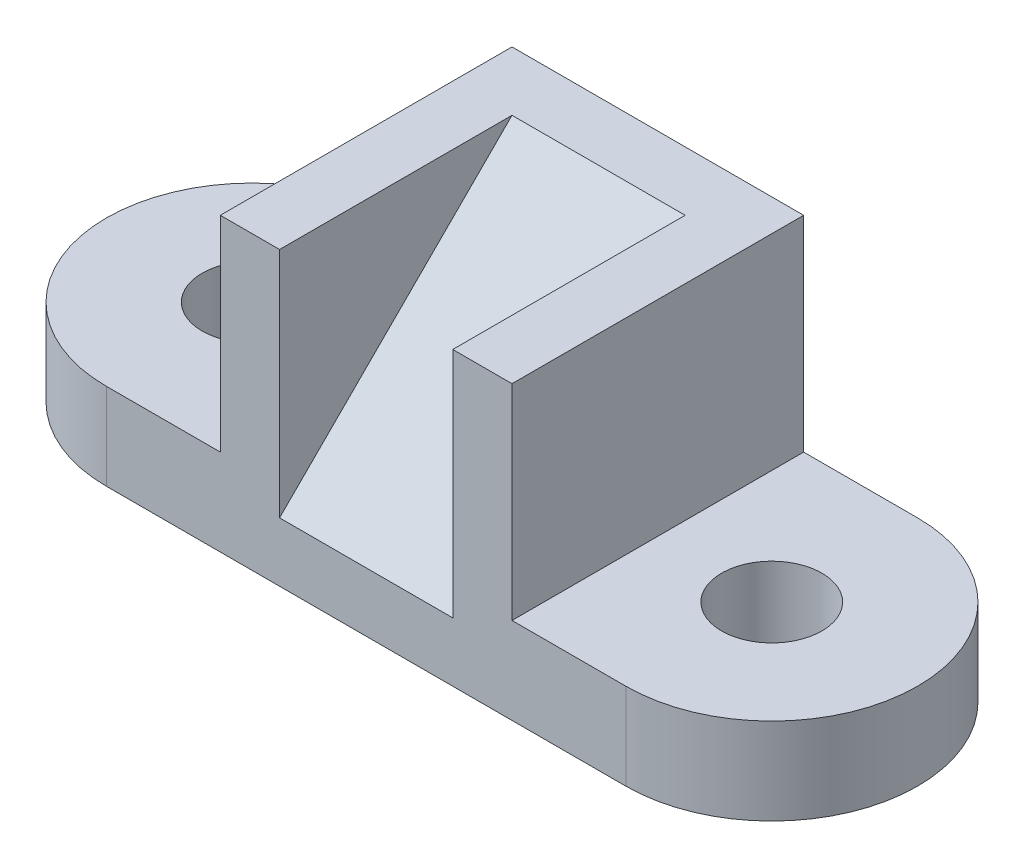
SolidWorks part; units mm, degrees
ref_plane "Front Plane" through (0, 0, 0) normal (0, 0, 1) x (1, 0, 0)
ref_plane "Top Plane" through (0, 0, 0) normal (0, 1, 0) x (1, 0, 0)
ref_plane "Right Plane" through (0, 0, 0) normal (1, 0, 0) x (0, 0, -1)
sketch "Sketch1" plane through (0, 0, 0) normal (0, 1, 0) x (1, 0, 0)
  line L0 (0, 0) -> (114, 0) construction
  line L1 (0, 32) -> (114, 32)
  line L2 (0, -32) -> (114, -32)
  arc A0 (0, 32) -> (0, -32) centre (0, 0) ccw
  arc A1 (114, -32) -> (114, 32) centre (114, 0) ccw
  dimension "D1" = 64
  dimension "D2" = 114
extrude "Boss-Extrude1" add sketch "Sketch1" along normal blind 19
sketch "Sketch2" plane through (0, 19, 0) normal (0, 1, 0) x (1, 0, 0)
  line L0 (0, 0) -> (114, 0) construction
  circle A0 centre (0, 0) radius 11
  circle A1 centre (114, 0) radius 11
  dimension "D1" = 22
  dimension "D2" = 114
extrude "Cut-Extrude1" cut sketch "Sketch2" against normal blind 19
sketch "Sketch3" plane through (0, 19, 0) normal (0, 1, 0) x (1, 0, 0)
  line L0 (-32, 0) -> (146, 0) construction
  line L1 (57, 32) -> (57, -32) construction
  line L2 (0, -32) -> (114, -32) construction
  line L3 (89, 32) -> (89, -32)
  line L4 (89, 32) -> (25, 32)
  line L6 (89, -32) -> (25, -32)
  line L7 (25, 32) -> (25, -32)
  arc A0 (0, 32) -> (0, -32) centre (0, 0) ccw construction
  arc A1 (114, -32) -> (114, 32) centre (114, 0) ccw construction
  point P13 (57, 0)
  dimension "D1" = 64
extrude "Boss-Extrude2" add sketch "Sketch3" along normal blind 45
sketch "Sketch4" plane through (0, 0, 32) normal (0, 0, 1) x (1, 0, 0)
  line L0 (25, 64) -> (38, 64) construction
  line L1 (25, 64) -> (89, 64) construction
  line L2 (25, 41.5) -> (89, 41.5) construction
  line L3 (25, 64) -> (25, 19) construction
  line L4 (89, 64) -> (89, 19) construction
  line L5 (57, 64) -> (57, 41.5) construction
  line L6 (57, 41.5) -> (57, 0) construction
  line L7 (0, 0) -> (114, 0) construction
  line L8 (89, 64) -> (76, 64) construction
  line L9 (89, 0) -> (89, 13) construction
  line L11 (38, 64) -> (76, 64)
  line L12 (38, 64) -> (38, 13)
  line L13 (38, 13) -> (76, 13)
  line L14 (76, 64) -> (76, 13)
  dimension "D1" = 38
  dimension "D2" = 51
sketch "Sketch5" plane through (0, 64, 0) normal (0, 1, 0) x (1, 0, 0)
  line L0 (57, 32) -> (57, 19) construction
  line L1 (89, 32) -> (25, 32) construction
  line L2 (25, 0) -> (38, 0) construction
  line L3 (25, 32) -> (25, -32) construction
  line L4 (89, 0) -> (76, 0) construction
  line L5 (89, -32) -> (89, 32) construction
  line L7 (38, 19) -> (76, 19)
  line L8 (38, 19) -> (38, -32)
  line L9 (38, -32) -> (76, -32)
  line L10 (76, 19) -> (76, -32)
  dimension "D1" = 38
  dimension "D2" = 51
sketch "Sketch7" plane through (0, 64, 0) normal (0, 1, 0) x (1, 0, 0)
  line L0 (38, 19) -> (25, 19) construction
  line L1 (25, 32) -> (25, -32) construction
sketch "Sketch10" plane through (0, 64, 0) normal (0, 1, 0) x (1, 0, 0)
  line L1 (38, 19) -> (76, 19)
  line L2 (38, 19) -> (38, -32)
  line L3 (38, -32) -> (76, -32)
  line L4 (76, 19) -> (76, -32)
extrude "Cut-Extrude2" cut sketch "Sketch10" against normal blind 51
sketch "Sketch11" plane through (76, 0, 0) normal (-1, 0, 0) x (0, 0, 1)
  line L0 (-19, 64) -> (32, 13)
  line L1 (32, 13) -> (-19, 13)
  line L2 (-19, 13) -> (-19, 64)
extrude "Boss-Extrude3" add sketch "Sketch11" along normal blind 38
